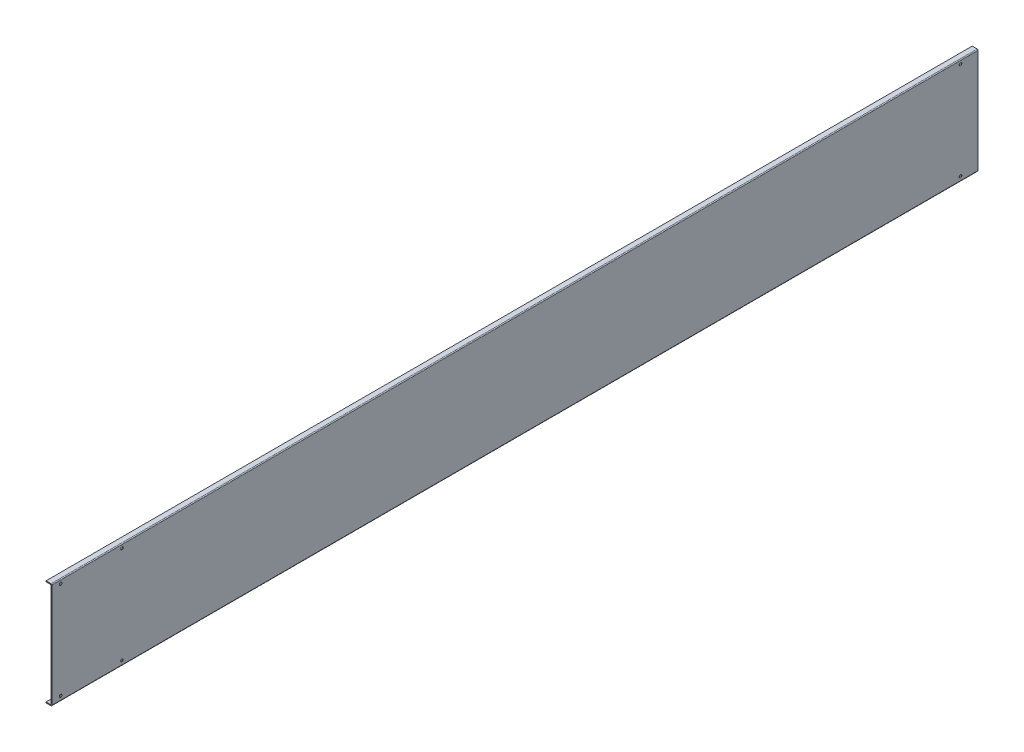
SolidWorks part; units mm, degrees
ref_plane "Front" through (0, 0, 0) normal (0, 0, 1) x (1, 0, 0)
ref_plane "Top" through (0, 0, 0) normal (0, 1, 0) x (1, 0, 0)
ref_plane "Right" through (0, 0, 0) normal (1, 0, 0) x (0, 0, -1)
sketch "Sketch1" plane through (0, 0, 0) normal (0, 0, 1) x (1, 0, 0)
  line L1 (-10, -1.5) -> (-10, 0)
  line L2 (0, -181) -> (-10, -181)
  line L3 (0, -181) -> (0, 0)
  line L4 (0, 0) -> (-10, 0)
  line L5 (-10, -181) -> (-10, -179.5)
  line L6 (-1.5, -179.5) -> (-10, -179.5)
  line L7 (-1.5, -179.5) -> (-1.5, -1.5)
  line L8 (-1.5, -1.5) -> (-10, -1.5)
  line L9 (-1.5, -1.5) -> (0, -1.5) construction
  dimension "D1" = 181
  dimension "D2" = 1.5
  dimension "D3" = 10
extrude "Boss-Extrude1" add sketch "Sketch1" against normal blind 1585
fillet "Fillet1" radius 1.5 2 edges at (0, -181, -792.5) (0, 0, -792.5)
hole_wizard "Ø4.5 (4.5) Diameter Hole1" positions "Sketch3" profile "Sketch2" hole size "Ø4.5" standard "JIS" end condition up to next
sketch "Sketch3" plane through (0, 0, 0) normal (1, 0, 0) x (0, 0, -1)
  point P0 (15, -7)
  point P8 (120, -7)
  point P10 (1555, -7)
  dimension "D1" = 15
  dimension "D2" = 105
  dimension "D3" = 1435
  dimension "D4" = 7
sketch "Sketch2" plane through (0, -7, -15) normal (0, 1, 0) x (0, 0, -1)
  line L0 (0, 0) -> (0, 1.5)
  line L1 (0, 1.5) -> (2.25, 1.5)
  line L2 (2.25, 1.5) -> (2.25, 0)
  line L5 (2.25, 0) -> (0, 0)
  line L11 (0, -6.35) -> (0, 107.95) construction
  dimension "Thru Hole Dia." = 4.5
  dimension "Thru Hole Depth" = 1.5
pattern_linear "LPattern2" count 2 spacing 166 along (0, -1, 0) of "Ø4.5 (4.5) Diameter Hole1"
